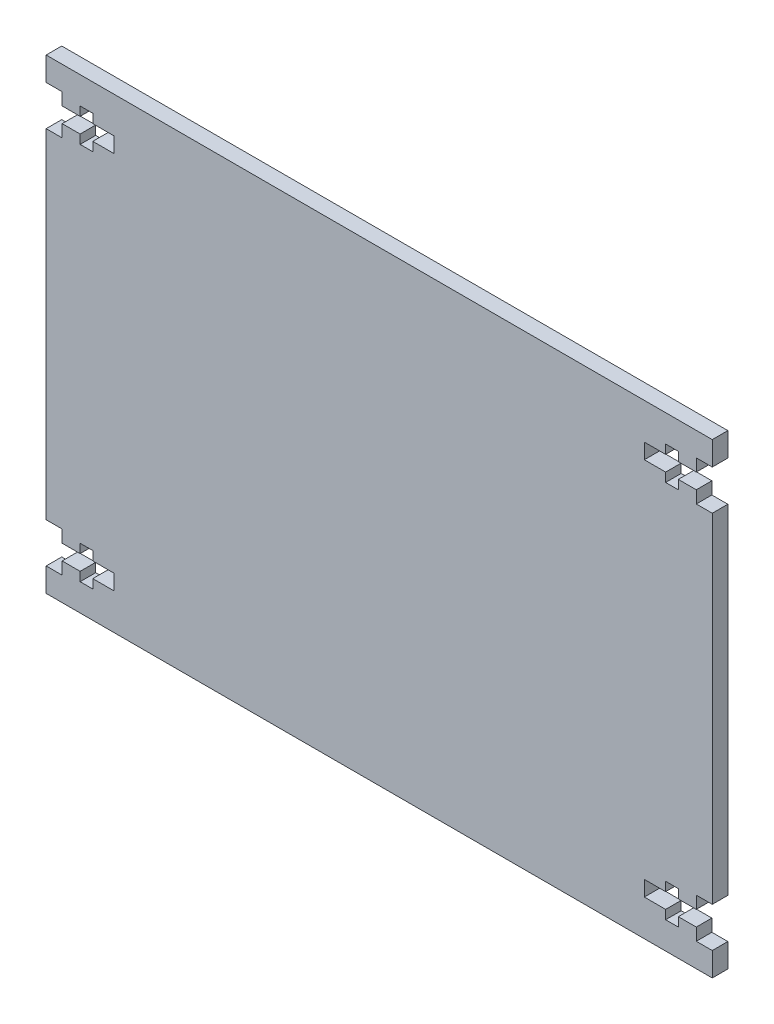
SolidWorks part; units mm, degrees
ref_plane "Front Plane" through (0, 0, 0) normal (0, 0, 1) x (1, 0, 0)
ref_plane "Top Plane" through (0, 0, 0) normal (0, 1, 0) x (1, 0, 0)
ref_plane "Right Plane" through (0, 0, 0) normal (1, 0, 0) x (0, 0, -1)
sketch "Sketch1" plane through (0, 0, 0) normal (0, 0, 1) x (1, 0, 0)
  line L0 (38.2104, 44.45) -> (-168.2296, 44.45) construction
  line L1 (-127, 88.9) -> (0, 88.9)
  line L2 (-127, 88.9) -> (-127, 84.3614)
  line L3 (-127, 0) -> (0, 0)
  line L4 (0, 88.9) -> (0, 84.3614)
  line L5 (-63.5, 114.8433) -> (-63.5, -14.2688) construction
  line L6 (0, 76.7414) -> (0, 12.1586)
  line L7 (0, 84.3614) -> (-3.048, 84.3614)
  line L8 (0.2852, 80.5514) -> (-12.954, 80.5514) construction
  line L9 (0, 76.7414) -> (-3.048, 76.7414)
  line L10 (-3.048, 84.3614) -> (-3.048, 82.0119)
  line L11 (-3.048, 82.0119) -> (-6.477, 82.0119)
  line L12 (-12.954, 82.0119) -> (-12.954, 79.0909)
  line L13 (-12.954, 79.0909) -> (-8.89, 79.0909)
  line L14 (-3.048, 79.0909) -> (-3.048, 76.7414)
  line L15 (-8.89, 83.7264) -> (-6.477, 83.7264)
  line L16 (-8.89, 83.7264) -> (-8.89, 82.0119)
  line L17 (-8.89, 77.3764) -> (-6.477, 77.3764)
  line L18 (-6.477, 83.7264) -> (-6.477, 82.0119)
  line L19 (-8.89, 82.0119) -> (-12.954, 82.0119)
  line L20 (-6.477, 79.0909) -> (-3.048, 79.0909)
  line L21 (-6.477, 79.0909) -> (-6.477, 77.3764)
  line L22 (-8.89, 79.0909) -> (-8.89, 77.3764)
  line L23 (0.2852, 8.3486) -> (-12.954, 8.3486) construction
  line L24 (-8.89, 9.8091) -> (-8.89, 11.5236)
  line L25 (-6.477, 9.8091) -> (-6.477, 11.5236)
  line L26 (-6.477, 9.8091) -> (-3.048, 9.8091)
  line L27 (-8.89, 6.8881) -> (-12.954, 6.8881)
  line L28 (-6.477, 5.1736) -> (-6.477, 6.8881)
  line L29 (-8.89, 11.5236) -> (-6.477, 11.5236)
  line L30 (-8.89, 5.1736) -> (-8.89, 6.8881)
  line L31 (-8.89, 5.1736) -> (-6.477, 5.1736)
  line L32 (-3.048, 9.8091) -> (-3.048, 12.1586)
  line L33 (-12.954, 9.8091) -> (-8.89, 9.8091)
  line L34 (-12.954, 6.8881) -> (-12.954, 9.8091)
  line L35 (-3.048, 6.8881) -> (-6.477, 6.8881)
  line L36 (-3.048, 4.5386) -> (-3.048, 6.8881)
  line L37 (0, 12.1586) -> (-3.048, 12.1586)
  line L38 (0, 4.5386) -> (-3.048, 4.5386)
  line L39 (-127.2852, 8.3486) -> (-114.046, 8.3486) construction
  line L40 (-127.2852, 80.5514) -> (-114.046, 80.5514) construction
  line L41 (-127, 4.5386) -> (-123.952, 4.5386)
  line L42 (-127, 12.1586) -> (-123.952, 12.1586)
  line L43 (-123.952, 4.5386) -> (-123.952, 6.8881)
  line L44 (-123.952, 6.8881) -> (-120.523, 6.8881)
  line L45 (-114.046, 6.8881) -> (-114.046, 9.8091)
  line L46 (-114.046, 9.8091) -> (-118.11, 9.8091)
  line L47 (-123.952, 9.8091) -> (-123.952, 12.1586)
  line L48 (-118.11, 5.1736) -> (-120.523, 5.1736)
  line L49 (-118.11, 5.1736) -> (-118.11, 6.8881)
  line L50 (-118.11, 11.5236) -> (-120.523, 11.5236)
  line L51 (-120.523, 5.1736) -> (-120.523, 6.8881)
  line L52 (-118.11, 6.8881) -> (-114.046, 6.8881)
  line L53 (-120.523, 9.8091) -> (-123.952, 9.8091)
  line L54 (-120.523, 9.8091) -> (-120.523, 11.5236)
  line L55 (-118.11, 9.8091) -> (-118.11, 11.5236)
  line L56 (-118.11, 79.0909) -> (-118.11, 77.3764)
  line L57 (-120.523, 79.0909) -> (-120.523, 77.3764)
  line L58 (-120.523, 79.0909) -> (-123.952, 79.0909)
  line L59 (-118.11, 82.0119) -> (-114.046, 82.0119)
  line L60 (-120.523, 83.7264) -> (-120.523, 82.0119)
  line L61 (-118.11, 77.3764) -> (-120.523, 77.3764)
  line L62 (-118.11, 83.7264) -> (-118.11, 82.0119)
  line L63 (-118.11, 83.7264) -> (-120.523, 83.7264)
  line L64 (-123.952, 79.0909) -> (-123.952, 76.7414)
  line L65 (-114.046, 79.0909) -> (-118.11, 79.0909)
  line L66 (-114.046, 82.0119) -> (-114.046, 79.0909)
  line L67 (-123.952, 82.0119) -> (-120.523, 82.0119)
  line L68 (-123.952, 84.3614) -> (-123.952, 82.0119)
  line L69 (-127, 76.7414) -> (-123.952, 76.7414)
  line L70 (-127, 84.3614) -> (-123.952, 84.3614)
  line L71 (-127, 76.7414) -> (-127, 12.1586)
  line L73 (0, 4.5386) -> (0, 0)
  line L74 (-127, 4.5386) -> (-127, 0)
  point P4 (0, 44.45)
  point P18 (-12.954, 80.5514)
  point P83 (-127, 44.45)
  dimension "D1" = 127
  dimension "D2" = 88.9
  dimension "D3" = 3.048
  dimension "D4" = 7.62
  dimension "D5" = 2.921
  dimension "D6" = 2.413
  dimension "D7" = 6.35
  dimension "D8" = 12.954
  dimension "D9" = 8.89
  dimension "D10" = 8.3486
extrude "Boss-Extrude1" add sketch "Sketch1" along normal blind 2.9718
